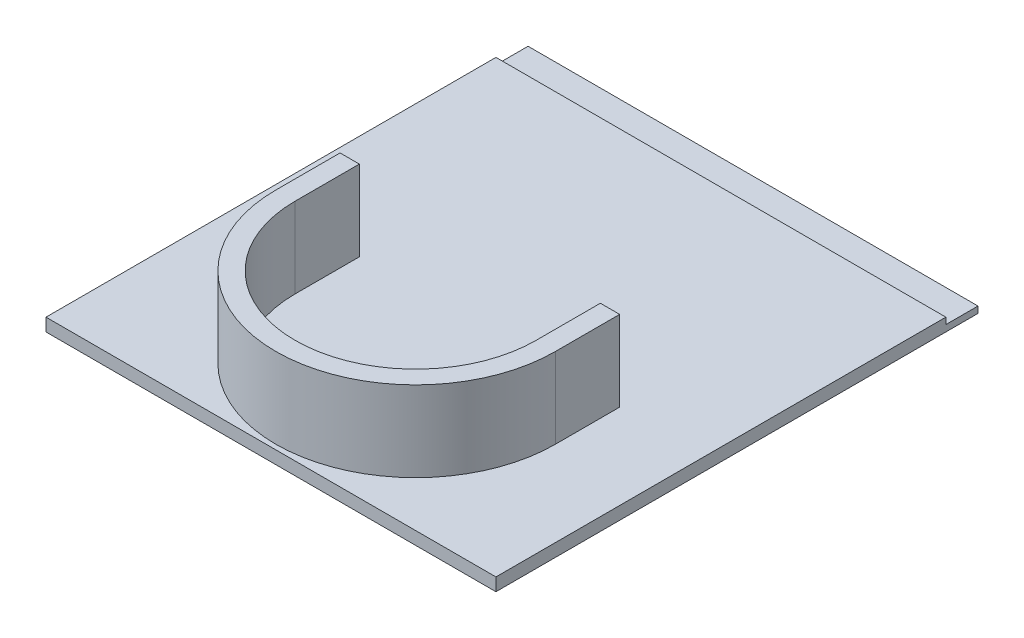
SolidWorks part; units mm, degrees
ref_plane "Front Plane" through (0, 0, 0) normal (0, 0, 1) x (1, 0, 0)
ref_plane "Top Plane" through (0, 0, 0) normal (0, 1, 0) x (1, 0, 0)
ref_plane "Right Plane" through (0, 0, 0) normal (1, 0, 0) x (0, 0, -1)
sketch "Sketch2" plane through (0, 0, 0) normal (0, 1, 0) x (1, 0, 0)
  line L0 (-70, 70) -> (70, 70) construction
  line L1 (-70, 210) -> (70, 210)
  line L2 (-70, 210) -> (-70, -210)
  line L3 (-70, -210) -> (70, -210)
  line L4 (70, 210) -> (70, -210)
  line L5 (-70, 210) -> (70, -210) construction
  line L6 (-70, -210) -> (70, 210) construction
  point P0 (0, 0)
  dimension "D1" = 420
  dimension "D2" = 140
  dimension "D3" = 280
extrude "Boss-Extrude1" add sketch "Sketch2" along normal blind 4
sketch "Sketch3" plane through (0, 4, 0) normal (0, 1, 0) x (1, 0, 0)
  line L0 (0, 0) -> (0, -210) construction
  line L1 (-37.5, -165) -> (-37.5, -145)
  line L2 (-37.5, -145) -> (-43.5, -145)
  line L3 (-43.5, -145) -> (-43.5, -165)
  line L4 (70, -210) -> (70, 210)
  line L5 (70, 210) -> (-70, 210)
  line L6 (-70, 210) -> (-70, -210)
  line L7 (-70, -210) -> (70, -210)
  line L8 (70, -210) -> (70, 210)
  line L9 (70, 210) -> (-70, 210)
  line L10 (-70, 210) -> (-70, -210)
  line L11 (-70, -210) -> (70, -210)
  line L12 (37.5, -165) -> (37.5, -145)
  line L13 (37.5, -145) -> (43.5, -145)
  line L14 (43.5, -145) -> (43.5, -165)
  line L15 (-37.5, -165) -> (37.5, -165) construction
  arc A0 (-37.5, -165) -> (37.5, -165) centre (0, -165) ccw
  arc A1 (-43.5, -165) -> (43.5, -165) centre (0, -165) ccw
  dimension "D2" = 37.5
  dimension "D3" = 6
  dimension "D4" = 6
  dimension "D5" = 45
  dimension "D6" = 6
  dimension "D7" = 20
  dimension "D8" = 20
  dimension "D1" = 0
extrude "Boss-Extrude2" add sketch "Sketch3" along normal blind 25 contours L3 A1 L14 L13 L12 A0 L1 L2
sketch "Sketch4" plane through (0, 4, 0) normal (0, 1, 0) x (1, 0, 0)
  line L1 (-65, 180) -> (-54.75, 180)
  line L2 (-65, 180) -> (-65, 99.75)
  line L3 (-65, 99.75) -> (-54.75, 99.75)
  line L4 (-54.75, 180) -> (-54.75, 99.75)
  line L5 (-65, 180) -> (-54.75, 99.75) construction
  line L6 (-65, 99.75) -> (-54.75, 180) construction
  line L7 (54.75, 180) -> (65, 180)
  line L8 (54.75, 180) -> (54.75, 99.75)
  line L9 (54.75, 99.75) -> (65, 99.75)
  line L10 (65, 180) -> (65, 99.75)
  line L11 (54.75, 180) -> (65, 99.75) construction
  line L12 (54.75, 99.75) -> (65, 180) construction
  line L13 (-70, 210) -> (70, 210) construction
  line L14 (-70, 210) -> (-70, -210) construction
  line L15 (70, 210) -> (70, -210) construction
  point P4 (-59.875, 139.875)
  point P9 (59.875, 139.875)
  dimension "D1" = 10.25
  dimension "D2" = 10.25
  dimension "D3" = 80.25
  dimension "D4" = 80.25
  dimension "D5" = 30
  dimension "D6" = 30
  dimension "D7" = 5
  dimension "D8" = 5
extrude "Cut-Extrude1" cut sketch "Sketch4" against normal blind 25.4
sketch "Sketch6" plane through (0, 4, 0) normal (0, 1, 0) x (1, 0, 0)
  line L0 (-65, 99.75) -> (-54.75, 99.75) construction
  line L1 (-65, 99.75) -> (-54.75, 99.75)
  line L2 (0, -202.5) -> (0, 99.75) construction
  line L3 (0, 99.75) -> (-54.75, 99.75) construction
  arc A0 (-37.5, -165) -> (37.5, -165) centre (0, -165) ccw construction
  arc A1 (-37.5, -165) -> (37.5, -165) centre (0, -165) ccw
  point P5 (0, -202.5)
  dimension "D1" = 302.25
sketch "Sketch7" plane through (0, 4, 0) normal (0, 1, 0) x (1, 0, 0)
  line L0 (70, 210) -> (-70, 210) construction
  line L1 (-65, 205) -> (65, 205)
  line L2 (-65, 205) -> (-65, 195)
  line L3 (-65, 195) -> (65, 195)
  line L4 (65, 205) -> (65, 195)
  line L5 (-65, 205) -> (65, 195) construction
  line L6 (-65, 195) -> (65, 205) construction
  line L7 (-70, 210) -> (-70, -210) construction
  line L8 (70, -210) -> (70, 210) construction
  point P4 (0, 200)
  dimension "D1" = 5
  dimension "D2" = 5
  dimension "D3" = 5
  dimension "D4" = 10
extrude "Cut-Extrude2" cut sketch "Sketch7" against normal blind 2.45 contours L3 L4 L1 L2
sketch "Sketch8" plane through (0, 0, 0) normal (0, -1, 0) x (1, 0, 0)
  line L0 (-70, 70) -> (70, 70)
  line L1 (-70, -70) -> (70, -70)
  line L4 (70, -210) -> (70, 210)
  line L5 (70, 210) -> (-70, 210)
  line L6 (-70, 210) -> (-70, -210)
  line L7 (-70, -210) -> (70, -210)
  line L8 (70, -210) -> (70, 210)
  line L9 (70, 210) -> (-70, 210)
  line L10 (-70, 210) -> (-70, -210)
  line L11 (-70, -210) -> (70, -210)
  line M7 (-54.75, -180) -> (-65, -180)
  line M8 (-65, -180) -> (-65, -99.75)
  line M9 (-65, -99.75) -> (-54.75, -99.75)
  line M10 (-54.75, -99.75) -> (-54.75, -180)
  line M11 (65, -180) -> (54.75, -180)
  line M12 (54.75, -180) -> (54.75, -99.75)
  line M13 (54.75, -99.75) -> (65, -99.75)
  line M14 (65, -99.75) -> (65, -180)
  line M15 (70, -210) -> (70, 210)
  line M17 (-70, 210) -> (-70, -210)
  line M18 (-70, -210) -> (70, -210)
  dimension "D2" = 140
  dimension "D3" = 140
  dimension "D1" = 0
extrude "Cut-Extrude3" cut sketch "Sketch8" against normal through all both and the other way through all contours L1 M17 M18 M15 M14 M11 M12 M13 M10 M7 M8 M9 | L1 L0 M17 M15
sketch "Sketch9" plane through (0, 0, 0) normal (0, -1, 0) x (1, 0, 0)
  line L0 (70, 210) -> (70, 70) construction
  line L1 (-70, 70) -> (70, 70)
  line L2 (-70, 70) -> (-70, 60)
  line L3 (-70, 60) -> (70, 60)
  line L4 (70, 70) -> (70, 60)
  line L5 (-70, 70) -> (70, 60) construction
  line L6 (-70, 60) -> (70, 70) construction
  point P4 (0, 65)
  dimension "D1" = 10
extrude "Boss-Extrude3" add sketch "Sketch9" against normal blind 2 contours L3 L4 L1 L2
